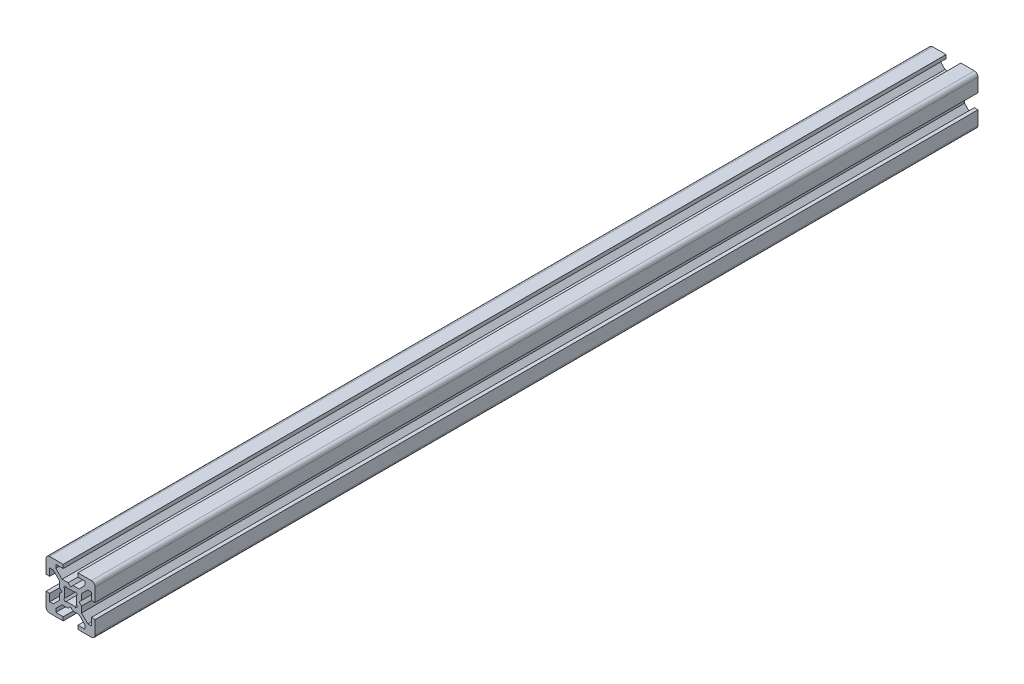
SolidWorks part; units mm, degrees
ref_plane "Front Plane" through (0, 0, 0) normal (0, 0, 1) x (1, 0, 0)
ref_plane "Top Plane" through (0, 0, 0) normal (0, 1, 0) x (1, 0, 0)
ref_plane "Right Plane" through (0, 0, 0) normal (1, 0, 0) x (0, 0, -1)
sketch "Sketch1" plane through (0, 0, 0) normal (0, 0, 1) x (1, 0, 0)
  line L0 (0, -1000) -> (0, 49000) construction
  line L1 (-1000, 0) -> (49000, 0) construction
  line L2 (0, 3.5) -> (1, 4.5)
  line L3 (1, 4.5) -> (3.4393, 4.5)
  line L4 (3.4393, 4.5) -> (6, 7.0607)
  line L5 (6, 7.0607) -> (6, 8.5)
  line L6 (6, 8.5) -> (3, 8.5)
  line L7 (3, 8.5) -> (3, 10)
  line L8 (3, 10) -> (10, 10)
  line L9 (0, 0) -> (35355.3391, 35355.3391) construction
  line L10 (-1.7929, 2.5) -> (1.7929, 2.5)
  line L11 (1.7929, 2.5) -> (2.1213, 2.8284)
  line L12 (2.1213, 2.8284) -> (2.8284, 2.1213)
  line L13 (2.5, 1.7929) -> (2.8284, 2.1213)
  line L14 (2.5, -1.7929) -> (2.5, 1.7929)
  line L15 (3.5, 0) -> (4.5, 1)
  line L16 (4.5, 1) -> (4.5, 3.4393)
  line L17 (4.5, 3.4393) -> (7.0607, 6)
  line L18 (7.0607, 6) -> (8.5, 6)
  line L19 (8.5, 6) -> (8.5, 3)
  line L20 (8.5, 3) -> (10, 3)
  line L21 (10, 3) -> (10, 10)
  line L22 (-3.5, 0) -> (-4.5, 1)
  line L23 (-2.5, -1.7929) -> (-2.5, 1.7929)
  line L24 (0, 3.5) -> (-1, 4.5)
  line L25 (-10, 3) -> (-10, 10)
  line L26 (-8.5, 3) -> (-10, 3)
  line L27 (-8.5, 6) -> (-8.5, 3)
  line L28 (-7.0607, 6) -> (-8.5, 6)
  line L29 (-4.5, 3.4393) -> (-7.0607, 6)
  line L30 (-4.5, 1) -> (-4.5, 3.4393)
  line L31 (-2.5, 1.7929) -> (-2.8284, 2.1213)
  line L32 (-2.1213, 2.8284) -> (-2.8284, 2.1213)
  line L33 (-1.7929, 2.5) -> (-2.1213, 2.8284)
  line L34 (-3, 10) -> (-10, 10)
  line L35 (-3, 8.5) -> (-3, 10)
  line L36 (-6, 8.5) -> (-3, 8.5)
  line L37 (-6, 7.0607) -> (-6, 8.5)
  line L38 (-3.4393, 4.5) -> (-6, 7.0607)
  line L39 (-1, 4.5) -> (-3.4393, 4.5)
  line L40 (8.5, -3) -> (10, -3)
  line L41 (8.5, -6) -> (8.5, -3)
  line L42 (7.0607, -6) -> (8.5, -6)
  line L43 (10, -3) -> (10, -10)
  line L44 (3, -10) -> (10, -10)
  line L45 (3, -8.5) -> (3, -10)
  line L46 (-3, -8.5) -> (-3, -10)
  line L47 (6, -8.5) -> (3, -8.5)
  line L48 (6, -7.0607) -> (6, -8.5)
  line L49 (3.4393, -4.5) -> (6, -7.0607)
  line L50 (4.5, -3.4393) -> (7.0607, -6)
  line L51 (4.5, -1) -> (4.5, -3.4393)
  line L52 (3.5, 0) -> (4.5, -1)
  line L53 (2.5, -1.7929) -> (2.8284, -2.1213)
  line L54 (2.1213, -2.8284) -> (2.8284, -2.1213)
  line L55 (1.7929, -2.5) -> (2.1213, -2.8284)
  line L56 (1, -4.5) -> (3.4393, -4.5)
  line L57 (0, -3.5) -> (1, -4.5)
  line L58 (-1, -4.5) -> (-3.4393, -4.5)
  line L59 (-3.4393, -4.5) -> (-6, -7.0607)
  line L60 (-6, -7.0607) -> (-6, -8.5)
  line L61 (-6, -8.5) -> (-3, -8.5)
  line L62 (-3, -10) -> (-10, -10)
  line L63 (-10, -3) -> (-10, -10)
  line L64 (-8.5, -3) -> (-10, -3)
  line L65 (-8.5, -6) -> (-8.5, -3)
  line L66 (-7.0607, -6) -> (-8.5, -6)
  line L67 (-4.5, -3.4393) -> (-7.0607, -6)
  line L68 (-4.5, -1) -> (-4.5, -3.4393)
  line L69 (-3.5, 0) -> (-4.5, -1)
  line L70 (-2.5, -1.7929) -> (-2.8284, -2.1213)
  line L71 (-2.1213, -2.8284) -> (-2.8284, -2.1213)
  line L72 (-1.7929, -2.5) -> (-2.1213, -2.8284)
  line L73 (-1.7929, -2.5) -> (1.7929, -2.5)
  line L74 (0, -3.5) -> (-1, -4.5)
  point P18 (2.4749, 2.4749)
  point P19 (4.5, 8.5)
  point P35 (0, 2.5)
  point P64 (2.5, 0)
  point P81 (-2.5, 0)
  dimension "D2" = 20
  dimension "D3" = 7
  dimension "D4" = 1.5
  dimension "D5" = 1.5
  dimension "D6" = 4
  dimension "D7" = 1
  dimension "D8" = 9
  dimension "D9" = 5
  dimension "D10" = 1
  dimension "D11" = 3.5
extrude "Boss-Extrude1" add sketch "Sketch1" along normal blind 360
fillet "Fillet1" radius 1.5 4 edges at (-10, -10, 180) (10, -10, 180) (10, 10, 180) (-10, 10, 180)
